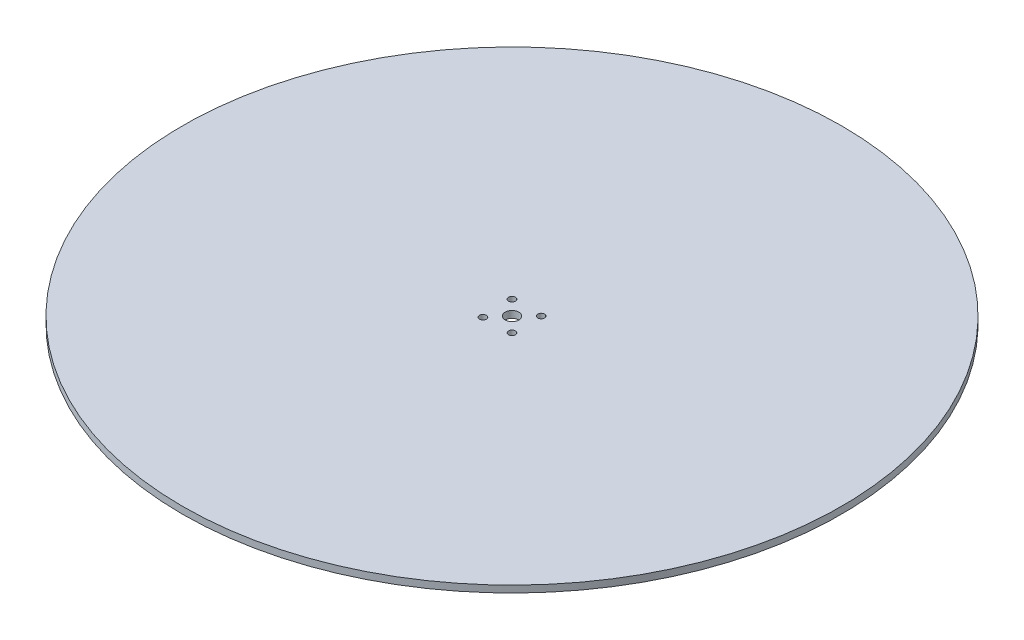
SolidWorks part; units mm, degrees
ref_plane "Front Plane" through (0, 0, 0) normal (0, 0, 1) x (1, 0, 0)
ref_plane "Top Plane" through (0, 0, 0) normal (0, 1, 0) x (1, 0, 0)
ref_plane "Right Plane" through (0, 0, 0) normal (1, 0, 0) x (0, 0, -1)
sketch "Sketch1" plane through (0, 0, 0) normal (0, 1, 0) x (1, 0, 0)
  circle A0 centre (0, 0) radius 152.4
extrude "Boss-Extrude1" add sketch "Sketch1" along normal blind 3.175
sketch "Sketch2" plane through (0, 3.175, 0) normal (0, 1, 0) x (1, 0, 0)
  circle A0 centre (0, 0) radius 3.175
  circle A1 centre (6.7352, 6.7352) radius 1.5875
  circle A2 centre (-6.7352, 6.7352) radius 1.5875
  circle A3 centre (-6.2402, -7.1963) radius 1.5875
  circle A4 centre (6.7352, -6.7352) radius 1.5875
extrude "Cut-Extrude1" cut sketch "Sketch2" against normal up to next
